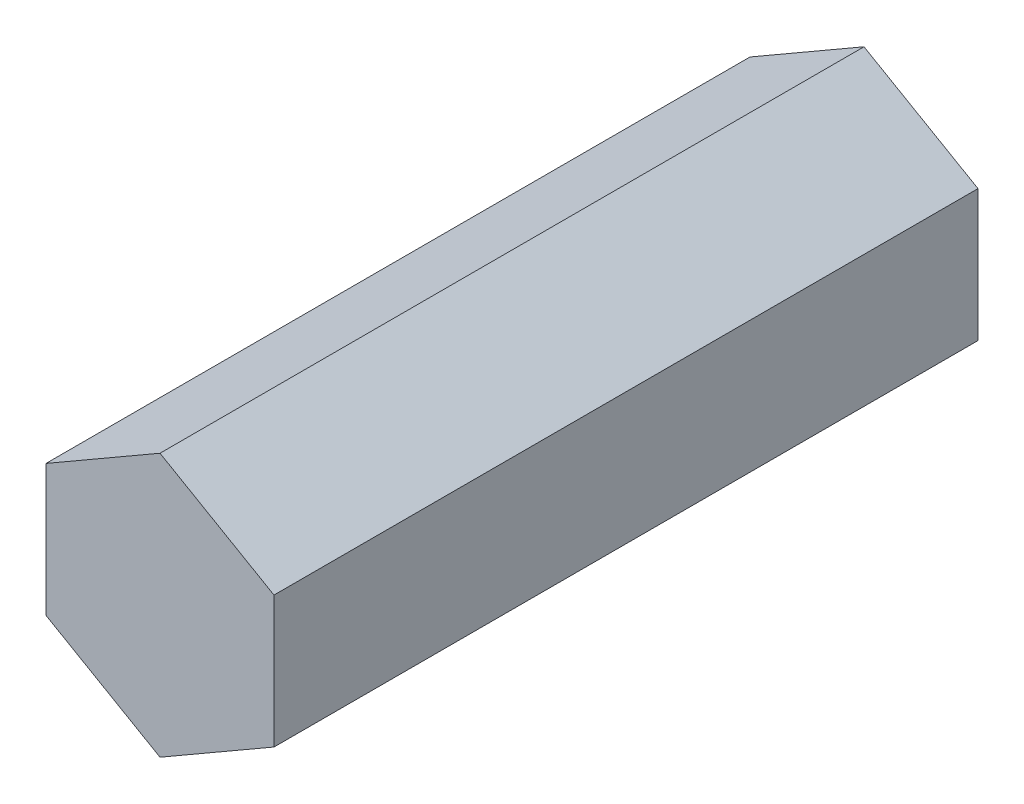
SolidWorks part; units mm, degrees
ref_plane "Front Plane" through (0, 0, 0) normal (0, 0, 1) x (1, 0, 0)
ref_plane "Top Plane" through (0, 0, 0) normal (0, 1, 0) x (1, 0, 0)
ref_plane "Right Plane" through (0, 0, 0) normal (1, 0, 0) x (0, 0, -1)
sketch "Sketch2" plane through (0, 0, 0) normal (0, 0, 1) x (1, 0, 0)
  line L0 (0, -89) -> (0, 89) construction
  line L7 (0, 89) -> (-77.0763, 44.5)
  line L8 (-77.0763, 44.5) -> (-77.0763, -44.5)
  line L9 (-77.0763, -44.5) -> (0, -89)
  line L10 (0, -89) -> (77.0763, -44.5)
  line L11 (77.0763, -44.5) -> (77.0763, 44.5)
  line L12 (77.0763, 44.5) -> (0, 89)
  line L21 (-89, 0) -> (89, 0) construction
  point P0 (0, 0)
  dimension "D1" = 89
  dimension "D2" = 178
  dimension "D3" = 154.1525
  dimension "D4" = 89
extrude "Boss-Extrude1" add sketch "Sketch2" along normal mid plane 476
